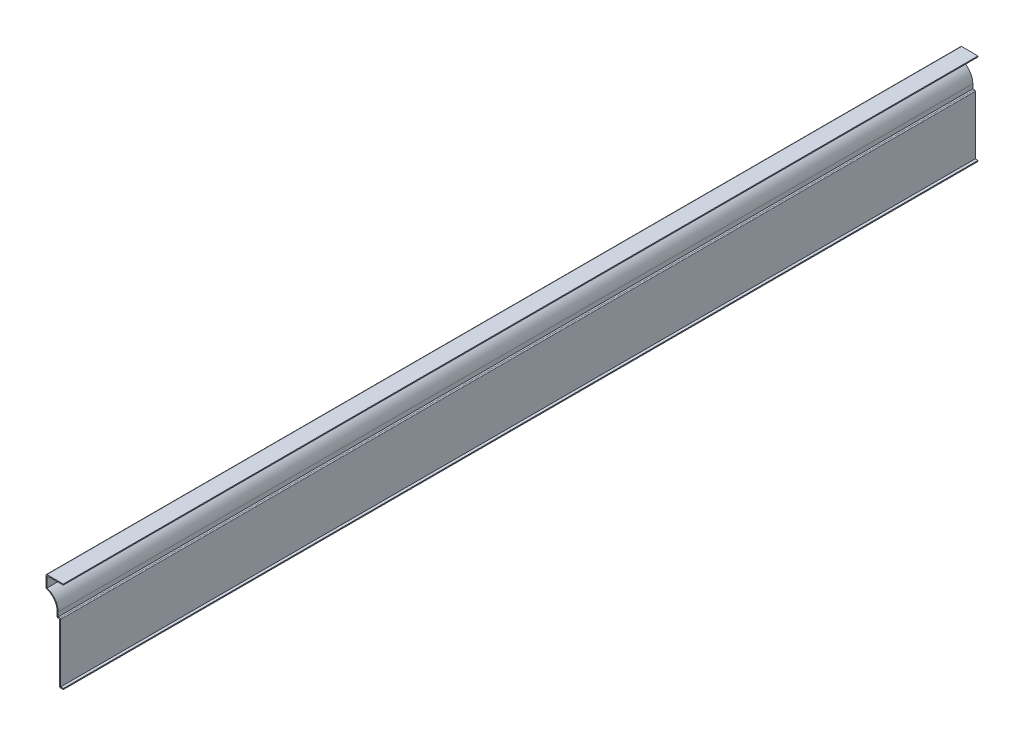
SolidWorks part; units mm, degrees
ref_plane "Front Plane" through (0, 0, 0) normal (0, 0, 1) x (1, 0, 0)
ref_plane "Top Plane" through (0, 0, 0) normal (0, 1, 0) x (1, 0, 0)
ref_plane "Right Plane" through (0, 0, 0) normal (1, 0, 0) x (0, 0, -1)
sketch "Sketch1" plane through (0, 0, 0) normal (0, 0, 1) x (1, 0, 0)
  line L0 (0, 0) -> (-4.7625, 0)
  line L1 (-4.7625, 0) -> (-4.7625, 76.2)
  line L2 (-4.7625, 76.2) -> (-7.9375, 76.2)
  line L3 (-7.9375, 76.2) -> (-7.9375, 83.1549)
  line L4 (-22.225, 101.6) -> (-22.225, 117.475)
  line L5 (-22.225, 117.475) -> (0, 117.475)
  arc A0 (-7.9375, 83.1549) -> (-22.225, 101.6) centre (-26.9875, 83.1549) ccw
  point P8 (0, 0)
  dimension "D4" = 19.05
  dimension "D1" = 4.7625
  dimension "D2" = 76.2
  dimension "D3" = 3.175
  dimension "D5" = 15.875
  dimension "D6" = 22.225
  dimension "D7" = 117.475
  dimension "D8" = 14.2875
  dimension "D9" = 25.4
extrude "Extrude-Thin1" add sketch "Sketch1" against normal blind 1174.75 thin
fillet "Fillet1" radius 1.27 5 edges at (-4.7625, 0, -587.375) (-3.4925, 77.47, -587.375) (-7.9375, 76.2, -587.375) (-22.225, 101.6, -587.375) (-22.225, 117.475, -587.375)
